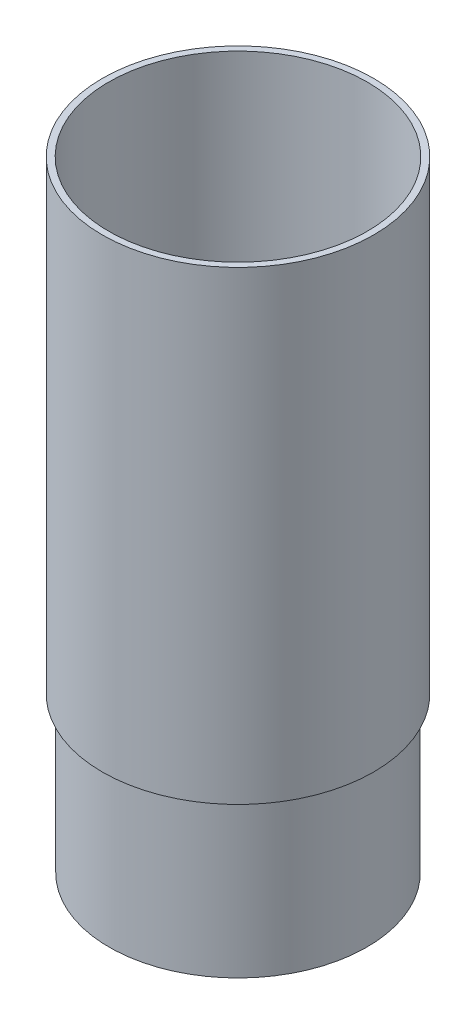
SolidWorks part; units mm, degrees
material "ABS"
ref_plane "Front Plane" through (0, 0, 0) normal (0, 0, 1) x (1, 0, 0)
ref_plane "Top Plane" through (0, 0, 0) normal (0, 1, 0) x (1, 0, 0)
ref_plane "Right Plane" through (0, 0, 0) normal (1, 0, 0) x (0, 0, -1)
sketch "Sketch1" plane through (0, 0, 0) normal (0, 0, 1) x (1, 0, 0)
  line L0 (0, 0) -> (0, 54.0332) construction
  line L1 (-20.0787, 0) -> (-20.0787, 27.3)
  line L2 (-20.0787, 27.3) -> (-21.1836, 31.4235)
  line L3 (-21.1836, 31.4235) -> (-21.1836, 101.6)
  line L4 (-21.1836, 101.6) -> (-22.225, 101.6)
  line L5 (-22.225, 101.6) -> (-22.225, 25.4)
  line L6 (-22.225, 25.4) -> (-21.1201, 25.4)
  line L7 (-21.1201, 25.4) -> (-21.1201, 0)
  line L8 (-21.1201, 0) -> (-20.0787, 0)
  dimension "D1" = 42.2402
  dimension "D2" = 44.45
  dimension "D3" = 25.4
  dimension "D4" = 101.6
  dimension "D5" = 1.0414
  dimension "D6" = 1.0414
  dimension "D7" = 15
  dimension "D8" = 1.9
revolve "Revolve1" add sketch "Sketch1" angle 360 mid plane about L0
